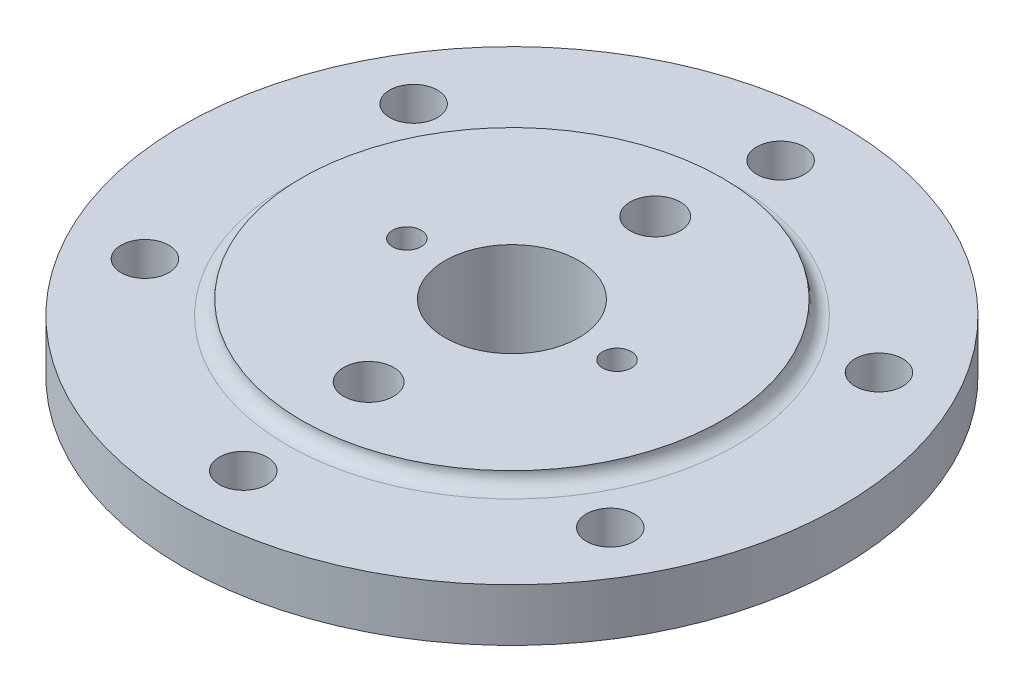
SolidWorks part; units mm, degrees
ref_plane "Front Plane" through (0, 0, 0) normal (0, 0, 1) x (1, 0, 0)
ref_plane "Top Plane" through (0, 0, 0) normal (0, 1, 0) x (1, 0, 0)
ref_plane "Right Plane" through (0, 0, 0) normal (1, 0, 0) x (0, 0, -1)
sketch "Sketch2" plane through (0, 0, 0) normal (1, 0, 0) x (0, 0, -1)
  line L0 (0, 70.4543) -> (0, -81) construction
  line L1 (28, 0) -> (88, 0)
  line L3 (94, -6) -> (138, -6)
  line L4 (138, -6) -> (138, -28)
  line L5 (138, -28) -> (81, -28)
  line L6 (81, -28) -> (81, -34)
  line L7 (81, -34) -> (35, -81)
  line L8 (35, -81) -> (14, -81)
  line L9 (28, 0) -> (28, -41.9171)
  line L10 (28, -41.9171) -> (14, -50)
  line L11 (14, -50) -> (14, -81)
  arc A0 (88, 0) -> (94, -6) centre (94, 0) ccw
  dimension "D13" = 12
  dimension "D1" = 138
  dimension "D2" = 22
  dimension "D3" = 70
  dimension "D4" = 81
  dimension "D5" = 88
  dimension "D6" = 6
  dimension "D7" = 28
  dimension "D8" = 60
  dimension "D9" = 14
  dimension "D10" = 47
  dimension "D11" = 6
  dimension "D12" = 50
revolve "Revolve1" add sketch "Sketch2" angle 360 about L0
sketch "Sketch4" plane through (0, -6, 0) normal (0, 1, 0) x (1, 0, 0)
  line L0 (0, 0) -> (0, 112.5) construction
  circle A0 centre (0, 112.5) radius 10
  circle A1 centre (97.4279, 56.25) radius 10
  circle A2 centre (97.4279, -56.25) radius 10
  circle A3 centre (0, -112.5) radius 10
  circle A4 centre (-97.4279, -56.25) radius 10
  circle A5 centre (-97.4279, 56.25) radius 10
  point P16 (0, 0)
  dimension "D2" = 20
  dimension "D1" = 112.5
  dimension "D3" = 6
extrude "Cut-Extrude1" cut sketch "Sketch4" against normal through all
hole_wizard "M24 Tapped Hole1" positions "Sketch5" profile "Sketch6" tap size "M24" standard "ISO"
sketch "Sketch5" plane through (0, 0, 0) normal (0, 1, 0) x (1, 0, 0)
  line L0 (0, 0) -> (0, 60) construction
  line L2 (0, 0) -> (0, -60) construction
  point P2 (0, 60)
  point P8 (0, -60)
  dimension "D1" = 60
  dimension "D2" = 60
sketch "Sketch6" plane through (0, 0, 60) normal (1, 0, 0) x (0, 0, 1)
  line L0 (0, 0) -> (0, 33.0622)
  line L1 (0, 33.0622) -> (10.5, 27)
  line L2 (10.5, 27) -> (10.5, 0)
  line L5 (10.5, 0) -> (0, 0)
  line L10 (0, 33.0622) -> (-10.5, 27) construction
  line L11 (0, -6.35) -> (0, 107.95) construction
  dimension "Tap Drill Dia." = 21
  dimension "Tap Drill Depth" = 27
  dimension "Drill Angle" = 120
cosmetic thread "Hole Thread1"
cosmetic thread "Hole Thread2"
hole_wizard "M12 Tapped Hole1" positions "Sketch9" profile "Sketch10" tap size "M12" standard "ISO"
sketch "Sketch9" plane through (0, 0, 0) normal (0, 1, 0) x (1, 0, 0)
  line L0 (-44, 0) -> (44, 0)
  point P1 (-44, 0)
  point P2 (44, 0)
  point P5 (0, 0)
  dimension "D1" = 88
sketch "Sketch10" plane through (-44, 0, 0) normal (1, 0, 0) x (0, 0, 1)
  line L0 (0, 0) -> (0, 18.4641)
  line L1 (0, 18.4641) -> (6, 15)
  line L2 (6, 15) -> (6, 0)
  line L5 (6, 0) -> (0, 0)
  line L10 (0, 18.4641) -> (-6, 15) construction
  line L11 (0, -6.35) -> (0, 107.95) construction
  dimension "Tap Drill Dia." = 12
  dimension "Tap Drill Depth" = 15
  dimension "Drill Angle" = 120
cosmetic thread "Hole Thread3"
cosmetic thread "Hole Thread4"
